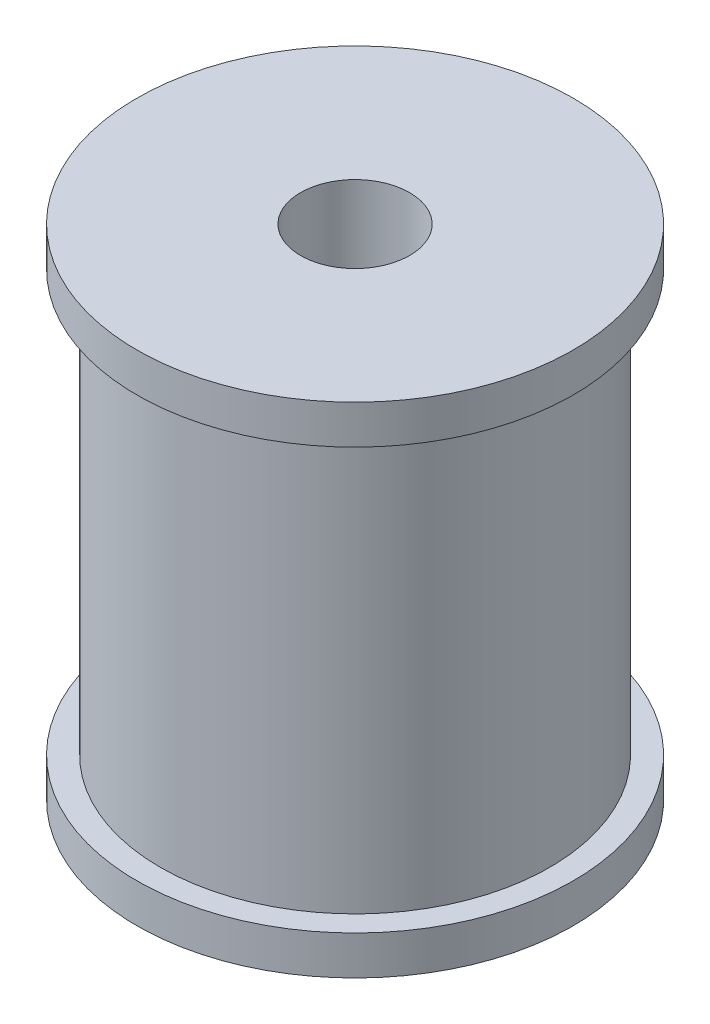
SolidWorks part; units mm, degrees
material "ABS"
ref_plane "Front Plane" through (0, 0, 0) normal (0, 0, 1) x (1, 0, 0)
ref_plane "Top Plane" through (0, 0, 0) normal (0, 1, 0) x (1, 0, 0)
ref_plane "Right Plane" through (0, 0, 0) normal (1, 0, 0) x (0, 0, -1)
sketch "Sketch3" plane through (0, 0, 0) normal (0, 0, 1) x (1, 0, 0)
  line L0 (0, 0) -> (0, 32) construction
  line L1 (0, 32) -> (3.5, 32) construction
  line L2 (3.5, 32) -> (3.5, 0)
  line L3 (3.5, 0) -> (0, 0) construction
  line L4 (3.5, 0) -> (14, 0)
  line L5 (14, 0) -> (14, 2.5)
  line L6 (14, 2.5) -> (12.5, 2.5)
  line L7 (12.5, 2.5) -> (12.5, 29.5)
  line L8 (12.5, 29.5) -> (14, 29.5)
  line L9 (14, 29.5) -> (14, 32)
  line L10 (14, 32) -> (3.5, 32)
  dimension "D1" = 25
  dimension "D2" = 27
  dimension "D3" = 32
  dimension "D4" = 1.5
  dimension "D5" = 7
revolve "Revolve1" add sketch "Sketch3" angle 360 about L0
